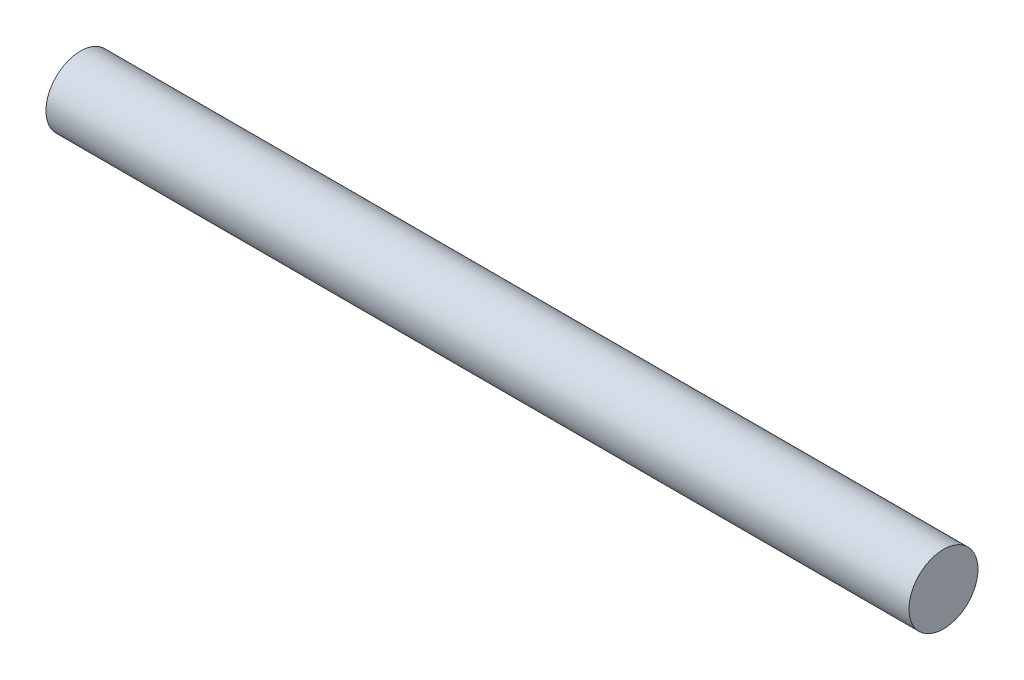
SolidWorks part; units mm, degrees
ref_plane "Front Plane" through (0, 0, 0) normal (0, 0, 1) x (1, 0, 0)
ref_plane "Top Plane" through (0, 0, 0) normal (0, 1, 0) x (1, 0, 0)
ref_plane "Right Plane" through (0, 0, 0) normal (1, 0, 0) x (0, 0, -1)
sketch "Sketch1" plane through (0, 0, 0) normal (1, 0, 0) x (0, 0, -1)
  circle A0 centre (0, 0) radius 2
  dimension "D1" = 4
extrude "Boss-Extrude1" add sketch "Sketch1" along normal blind 50
